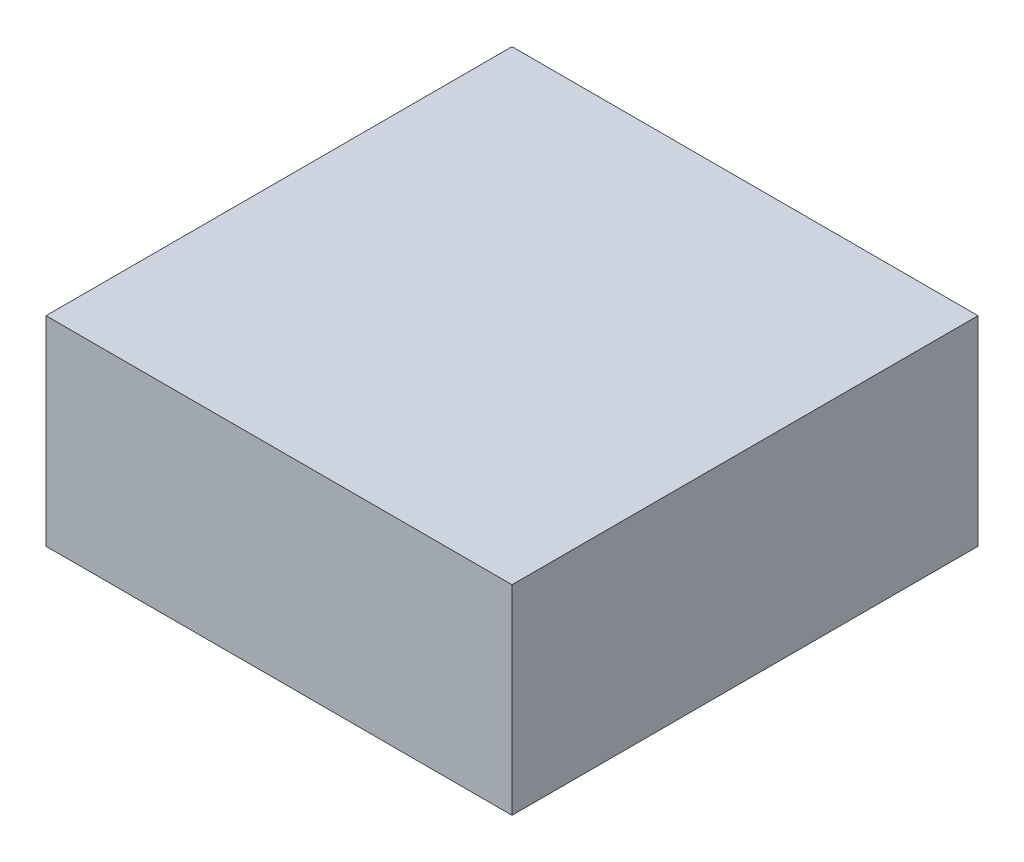
SolidWorks part; units mm, degrees
ref_plane "Front Plane" through (0, 0, 0) normal (0, 0, 1) x (1, 0, 0)
ref_plane "Top Plane" through (0, 0, 0) normal (0, 1, 0) x (1, 0, 0)
ref_plane "Right Plane" through (0, 0, 0) normal (1, 0, 0) x (0, 0, -1)
sketch "Sketch1" plane through (0, 0, 0) normal (0, 1, 0) x (1, 0, 0)
  line L1 (0, 0) -> (88.9, 0)
  line L2 (0, 0) -> (0, 88.9)
  line L3 (0, 88.9) -> (88.9, 88.9)
  line L4 (88.9, 0) -> (88.9, 88.9)
  dimension "D1" = 88.9
  dimension "D2" = 88.9
extrude "Boss-Extrude1" add sketch "Sketch1" along normal blind 38.1
